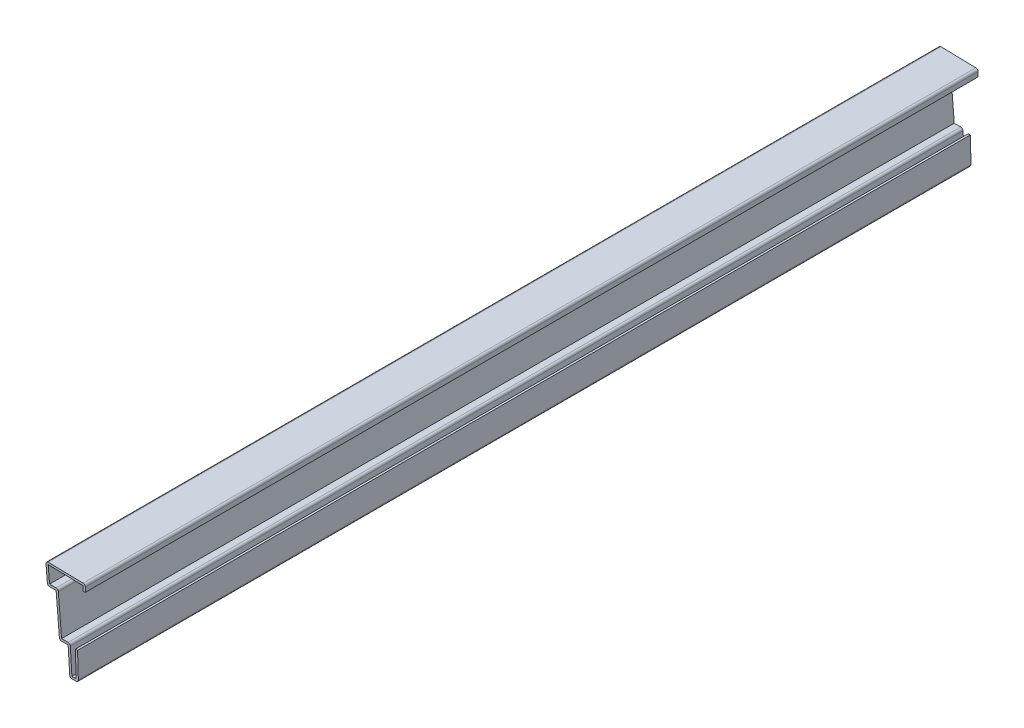
SolidWorks part; units mm, degrees
ref_plane "Front Plane" through (0, 0, 0) normal (0, 0, 1) x (1, 0, 0)
ref_plane "Top Plane" through (0, 0, 0) normal (0, 1, 0) x (1, 0, 0)
ref_plane "Right Plane" through (0, 0, 0) normal (1, 0, 0) x (0, 0, -1)
sketch "Sketch1" plane through (0, 0, 0) normal (0, 0, 1) x (1, 0, 0)
  line L0 (0, 0) -> (-0.3969, 12.7)
  line L1 (0, 0) -> (-3.9688, 0)
  line L2 (-3.9688, 0) -> (-4.7625, 12.7)
  line L3 (-4.7625, 12.7) -> (-8.7313, 12.7)
  line L4 (-8.7313, 12.7) -> (-10.3188, 31.75)
  line L5 (-10.3188, 31.75) -> (-14.2875, 31.75)
  line L6 (-14.2875, 31.75) -> (-15.0813, 41.275)
  line L7 (-15.0813, 41.275) -> (3.175, 40.8781)
  line L8 (3.175, 40.8781) -> (3.175, 37.7031)
  point P3 (-8.9165, 41.275)
  point P12 (-5.26, 13.4784)
  point P13 (-3.4024, 13.3389)
  point P14 (-2.2161, 0)
  point P15 (3.175, 38.6366)
  point P16 (-7.1605, 12.7)
  point P17 (-5.1668, 12.7)
  point P18 (-10.3171, 31.75)
  dimension "D1" = 41.275
  dimension "D2" = 18.2562
  dimension "D3" = 12.7
  dimension "D4" = 0.3969
  dimension "D5" = 3.175
  dimension "D6" = 0.3969
  dimension "D7" = 3.175
  dimension "D8" = 9.525
  dimension "D9" = 19.05
  dimension "D10" = 3.9688
  dimension "D11" = 0.7937
  dimension "D12" = 3.9688
  dimension "D13" = 1.5875
  dimension "D14" = 3.9688
extrude "Extrude-Thin1" add sketch "Sketch1" against normal blind 412.75 thin thin type one direction wall 1.016
fillet "Fillet1" radius 1.016 8 edges at (0, 0, -206.375) (-3.9688, 0, -206.375) (-3.808, 13.716, -206.375) (-8.7313, 12.7, -206.375) (-9.3839, 32.766, -206.375) (-14.2875, 31.75, -206.375) (-15.0813, 41.275, -206.375) (3.175, 40.8781, -206.375)
